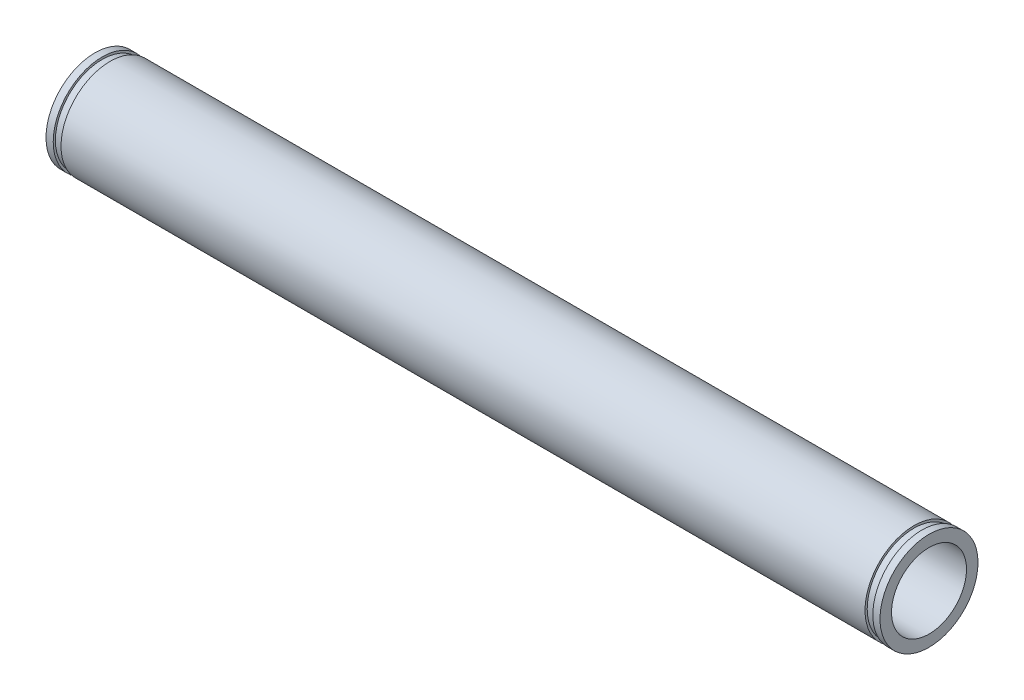
SolidWorks part; units mm, degrees
material "6061-T6 (SS)"
ref_plane "Front Plane" through (0, 0, 0) normal (0, 0, 1) x (1, 0, 0)
ref_plane "Top Plane" through (0, 0, 0) normal (0, 1, 0) x (1, 0, 0)
ref_plane "Right Plane" through (0, 0, 0) normal (1, 0, 0) x (0, 0, -1)
sketch "Sketch1" plane through (0, 0, 0) normal (1, 0, 0) x (0, 0, -1)
  circle A0 centre (0, 0) radius 4.7625
  circle A1 centre (0, 0) radius 6.223
  dimension "D1" = 12.446
  dimension "D2" = 9.525
extrude "Boss-Extrude1" add sketch "Sketch1" along normal mid plane 105.918
ref_plane "Plane1" through (-51.054, 0, 0) normal (-1, 0, 0) x (0, 0, 1)
sketch "Sketch2" plane through (-51.054, 0, 0) normal (-1, 0, 0) x (0, 0, 1)
  circle A0 centre (0, 0) radius 5.9436
  circle A1 centre (0, 0) radius 6.35
  dimension "D1" = 11.8872
  dimension "D2" = 12.7
extrude "Cut-Extrude1" cut sketch "Sketch2" along normal blind 0.9906
mirror "Mirror1" about plane through (0, 0, 0) normal (1, 0, 0) of "Cut-Extrude1"
